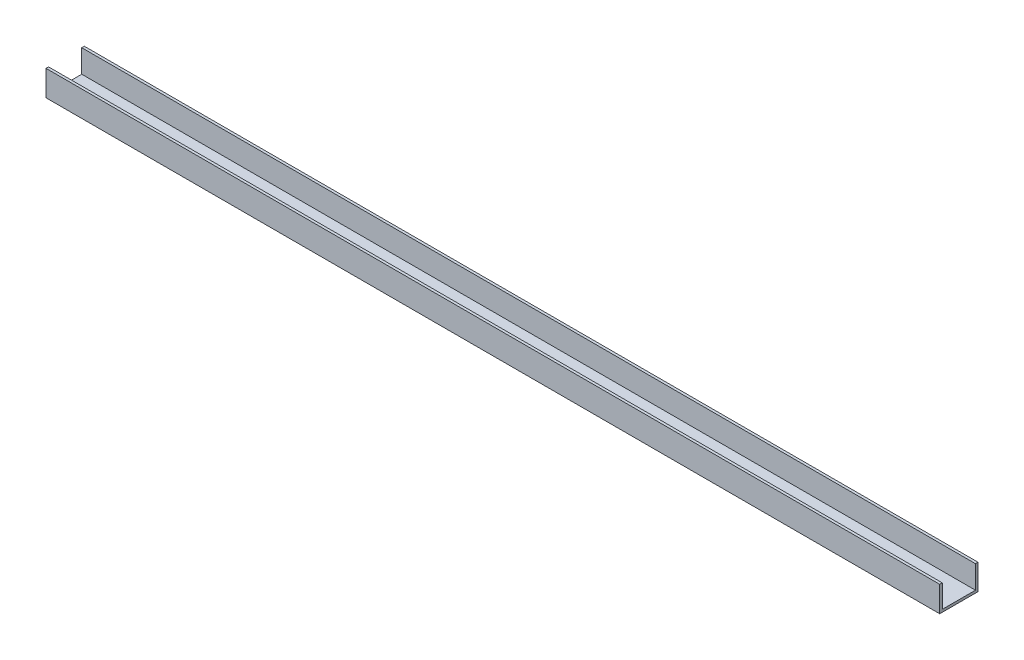
SolidWorks part; units mm, degrees
ref_plane "Front Plane" through (0, 0, 0) normal (0, 0, 1) x (1, 0, 0)
ref_plane "Top Plane" through (0, 0, 0) normal (0, 1, 0) x (1, 0, 0)
ref_plane "Right Plane" through (0, 0, 0) normal (1, 0, 0) x (0, 0, -1)
sketch "Sketch2" plane through (0, 0, 0) normal (0, 1, 0) x (1, 0, 0)
  line L1 (39.4836, 129.94) -> (389.4836, 129.94)
  line L2 (39.4836, 129.94) -> (39.4836, 114.94)
  line L3 (39.4836, 114.94) -> (389.4836, 114.94)
  line L4 (389.4836, 129.94) -> (389.4836, 114.94)
extrude "Boss-Extrude1" add sketch "Sketch2" along normal blind 10
sketch "Sketch3" plane through (0, 10, 0) normal (0, 1, 0) x (1, 0, 0)
  line L0 (389.4836, 115.94) -> (39.4836, 115.94)
  line L1 (389.4836, 114.94) -> (389.4836, 129.94) construction
  line L2 (39.4836, 129.94) -> (39.4836, 114.94) construction
  line L3 (389.4836, 129.94) -> (389.4836, 128.94)
  line L4 (389.4836, 128.94) -> (39.4836, 128.94)
  line L6 (39.4836, 115.94) -> (39.4836, 128.94)
  line L7 (389.4836, 115.94) -> (389.4836, 128.94)
  line M1 (39.4836, 129.94) -> (39.4836, 114.94)
  line M3 (389.4836, 114.94) -> (389.4836, 129.94)
extrude "Cut-Extrude1" cut sketch "Sketch3" against normal blind 9 contours L4 L0 M3 M1
sketch "Sketch4" plane through (0, 1, 0) normal (0, 1, 0) x (1, 0, 0)
  circle A0 centre (59.4836, 122.44) radius 2.4
  circle A1 centre (359.4836, 122.44) radius 2.5
extrude "Cut-Extrude3" cut sketch "Sketch4" against normal blind 10
